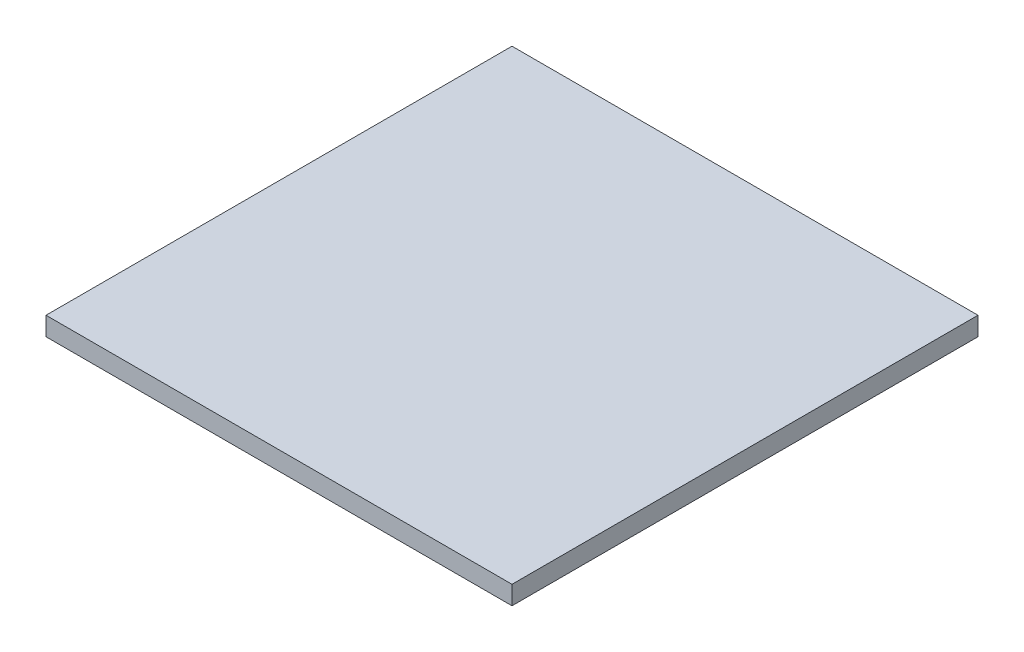
SolidWorks part; units mm, degrees
ref_plane "前视基准面" through (0, 0, 0) normal (0, 0, 1) x (1, 0, 0)
ref_plane "上视基准面" through (0, 0, 0) normal (0, 1, 0) x (1, 0, 0)
ref_plane "右视基准面" through (0, 0, 0) normal (1, 0, 0) x (0, 0, -1)
sketch "草图1" plane through (0, 0, 0) normal (0, 1, 0) x (1, 0, 0)
  line L1 (-25, 25) -> (25, 25)
  line L2 (-25, 25) -> (-25, -25)
  line L3 (-25, -25) -> (25, -25)
  line L4 (25, 25) -> (25, -25)
  line L5 (-25, 25) -> (25, -25) construction
  line L6 (-25, -25) -> (25, 25) construction
  point P0 (0, 0)
  dimension "D1" = 50
  dimension "D2" = 50
extrude "凸台-拉伸1" add sketch "草图1" along normal blind 2
